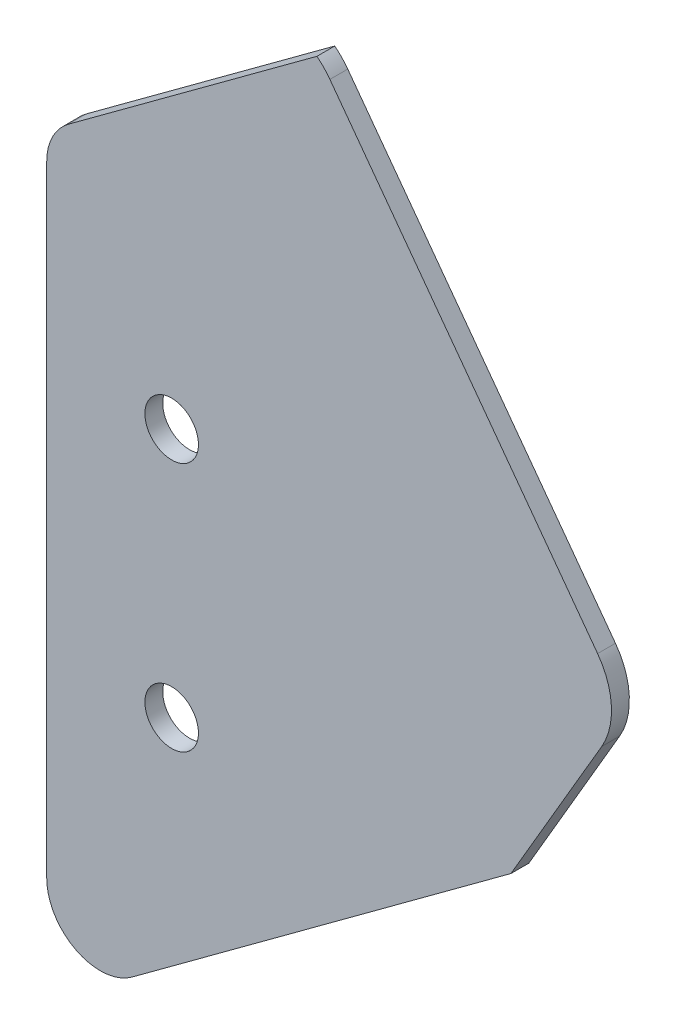
SolidWorks part; units mm, degrees
ref_plane "Front Plane" through (0, 0, 0) normal (0, 0, 1) x (1, 0, 0)
ref_plane "Top Plane" through (0, 0, 0) normal (0, 1, 0) x (1, 0, 0)
ref_plane "Right Plane" through (0, 0, 0) normal (1, 0, 0) x (0, 0, -1)
sketch "Sketch1" plane through (0, 0, 0) normal (0, 0, 1) x (1, 0, 0)
  line L3 (63.7105, 415.2372) -> (111.3328, 350.5861)
  line L5 (189.6651, 389.8722) -> (136.9407, 461.4498)
  line L6 (189.6651, 389.8722) -> (136.9407, 461.4498)
  line L7 (28.509, 259.3339) -> (187.6451, 376.5542)
  line L12 (112.073, 336.6473) -> (34.1431, 203.2651)
  line L13 (10.4775, 209.6718) -> (10.4775, 290.4204)
  line L24 (28.509, 259.3339) -> (187.6451, 376.5542)
  line L25 (13.335, 377.4175) -> (13.335, 267.0029)
  line L26 (13.335, 377.4175) -> (13.335, 267.0029)
  line L27 (123.6226, 463.4698) -> (17.211, 385.0865)
  line L28 (123.6226, 463.4698) -> (17.211, 385.0865)
  circle A0 centre (35.56, 347.2876) radius 4.7625 construction
  circle A1 centre (35.56, 347.2876) radius 4.7625
  circle A2 centre (35.56, 302.8376) radius 4.7625 construction
  circle A3 centre (35.56, 302.8376) radius 4.7625
  arc A12 (34.1431, 203.2651) -> (10.4775, 209.6718) centre (23.1775, 209.6718) cw
  arc A13 (63.7105, 415.2372) -> (45.9531, 417.9305) centre (53.4852, 407.7051) ccw
  arc A14 (112.073, 336.6473) -> (111.3328, 350.5861) centre (101.1074, 343.054) ccw
  arc A30 (13.335, 267.0029) -> (28.509, 259.3339) centre (22.86, 267.0029) ccw
  arc A31 (13.335, 267.0029) -> (28.509, 259.3339) centre (22.86, 267.0029) ccw
  arc A32 (17.211, 385.0865) -> (13.335, 377.4175) centre (22.86, 377.4175) ccw
  arc A33 (17.211, 385.0865) -> (13.335, 377.4175) centre (22.86, 377.4175) ccw
  arc A34 (136.9407, 461.4498) -> (123.6226, 463.4698) centre (129.2717, 455.8008) ccw
  arc A35 (136.9407, 461.4498) -> (123.6226, 463.4698) centre (129.2717, 455.8008) ccw
  arc A36 (187.6451, 376.5542) -> (189.6651, 389.8722) centre (181.996, 384.2232) ccw
  arc A37 (187.6451, 376.5542) -> (189.6651, 389.8722) centre (181.996, 384.2232) ccw
  dimension "D2" = 12.7
  dimension "D3" = 12.7
  dimension "D1" = 0
extrude "Boss-Extrude1" add sketch "Sketch1" along normal blind 3.175
